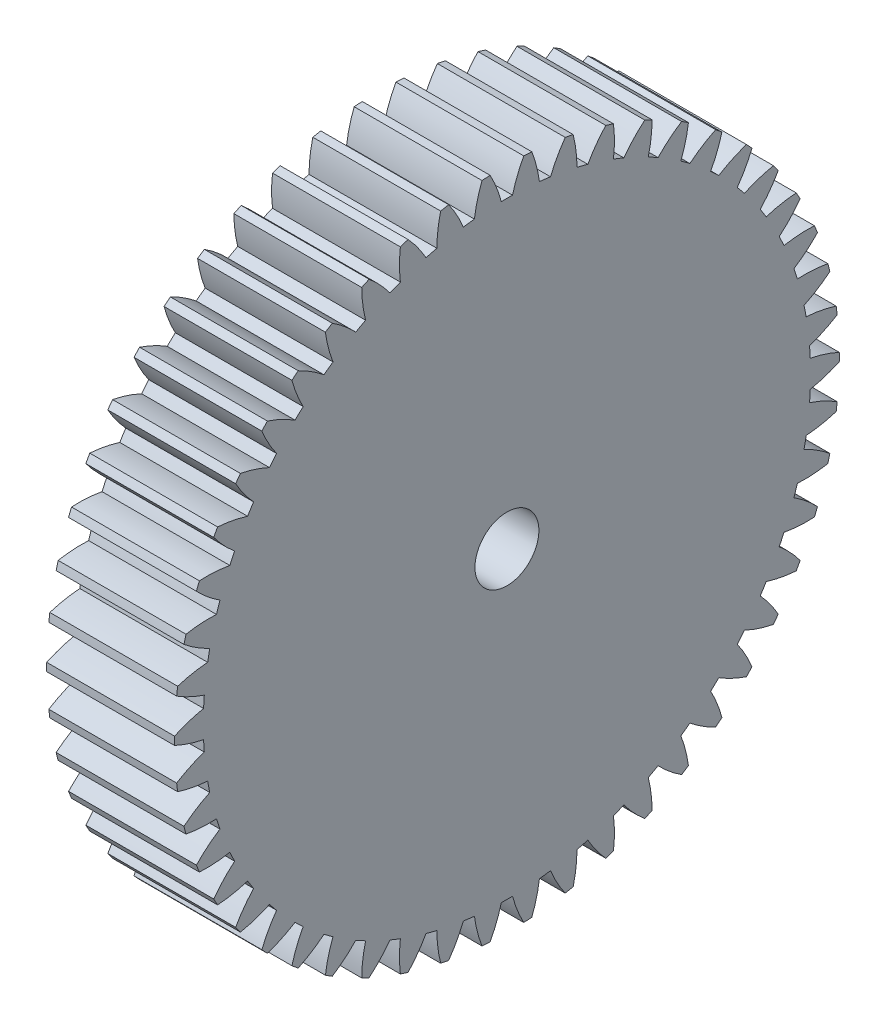
SolidWorks part; units mm, degrees
ref_plane "Plane1" through (0, 0, 0) normal (0, 0, 1) x (1, 0, 0)
ref_plane "Plane2" through (0, 0, 0) normal (0, 1, 0) x (1, 0, 0)
ref_plane "Plane3" through (0, 0, 0) normal (1, 0, 0) x (0, 0, -1)
other "Configuration Table"
sketch "HoldingSke" plane through (0, 0, 0) normal (0, 1, 0) x (1, 0, 0)
  line L0 (0, 0) -> (0.6428, -0.766)
  line L1 (-15, 0) -> (100, 0) construction
  line L2 (0, 0) -> (-2.1039, 2.3779)
  line L3 (0, 0) -> (-11.863, 4.5341)
  line L4 (0, 0) -> (5.5511, 6.6156)
  line L5 (0, 0) -> (-46.8476, -17.4728)
  line L6 (0, 0) -> (-8.2896, -5.593)
  line L7 (-2.1039, 2.3779) -> (8.6586, 51.2059)
  line L8 (-76.2, 54.61) -> (-75.3, 54.61)
  line L9 (-71.009, 38.7566) -> (-53.1078, 45.2721)
  line L10 (-76.2, 71.12) -> (104.1128, 71.12)
  line L11 (0, 0) -> (-10, 0)
  line L12 (-76.2, 101.6) -> (-76.162, 101.6)
  line L13 (24.9733, 27.94) -> (52.9518, 28.4284)
  line L14 (24.9733, 27.94) -> (24.9743, 27.94)
  line L15 (24.9733, 27.94) -> (100.4006, 29.5858)
  line L16 (-63.627, -1) -> (-12.827, -1)
  circle A0 centre (0, 0) radius 2.5
  circle A1 centre (0, 0) radius 23.749
  circle A2 centre (0, 0) radius 37.5
  circle A3 centre (0, 0) radius 2.5
  dimension "MHD" = 47.498
  dimension "Hub_dia" = 75
  dimension "Bore" = 5
  dimension "MBD" = 5
  dimension "Num_teeth" = 50
  dimension "Pitch" = 1
  dimension "Overall_len" = 50
  dimension "Show_teeth" = 50
  dimension "Thickness" = 10
  dimension "OAL" = 50.0001
  dimension "T_dim" = 0.9
  dimension "Ap" = 20
  dimension "H" = 19.05
  dimension "Pitch_radius" = 180.3128
  dimension "Width" = 10
  dimension "Backlash" = 0.038
  dimension "Addendum_fac" = 1
  dimension "Dedendum_fac" = 1.25
  dimension "Clearance_fac" = 0.25
  dimension "Dedendum_add" = 0.001
  dimension "Module" = 1
sketch "BasProSke" plane through (0, 0, 0) normal (0, 1, 0) x (1, 0, 0)
  line L0 (-10, 0) -> (60, 0) construction
  line L1 (0, 0) -> (0, 26)
  line L2 (0, 0) -> (10, 0)
  line L3 (10, 0) -> (10, 26)
  line L4 (10, 26) -> (0, 26)
  dimension "Thickness" = 10
  dimension "Diameter" = 52
revolve "Base-Revolve" add sketch "BasProSke" angle 360 about L0
sketch "TooCutSke" plane through (0, 0, 0) normal (1, 0, 0) x (0, 0, -1)
  line L1 (0, 0) -> (0, 107) construction
  line L2 (0, 0) -> (-0.8518, 24.9855) construction
  line L3 (0, 0) -> (-3.1382, 49.8807) construction
  line L4 (-0.8518, 24.9855) -> (-1.5691, 24.9404) construction
  arc A0 (0.4377, 23.745) -> (-0.4377, 23.745) centre (0, 0) ccw
  arc A1 (1.3294, 25.9914) -> (-1.3294, 25.9914) centre (0, 0) ccw
  circle A2 centre (0, 0) radius 25 construction
  circle A3 centre (0, 0) radius 23.4923 construction
  arc A4 (-0.4377, 23.745) -> (-1.3294, 25.9914) centre (-10.1099, 21.2056) ccw
  arc A5 (1.3294, 25.9914) -> (0.4377, 23.745) centre (10.1099, 21.2056) ccw
  dimension "Root_dia" = 47.498
  dimension "Overcut_dia" = 52.0508
  dimension "Pitch_dia" = 50
  dimension "Base_dia" = 46.9846
  dimension "Flank_rad" = 10
  dimension "Half_ang" = 3.6
  dimension "Half_CT" = 0.7188
extrude "ToothCut" cut sketch "TooCutSke" along normal through all
fillet "Breaks" [suppressed] radius 0.02
fillet "RootFillets" [suppressed] radius 0.251
pattern_circular "TeethCuts" count 50 every 7.2 about axis through (-10, 0, 0) along (1, 0, 0) of "ToothCut", "RootFillets", "Breaks"
sketch "HubNeaOneSke" plane through (0, 0, 0) normal (-1, 0, 0) x (0, 0, 1)
  circle A0 centre (0, 0) radius 23.749
  dimension "Diameter" = 47.498
extrude "HubNearOne" [suppressed] add sketch "HubNeaOneSke" along normal blind 40.0001
sketch "HubNeaBotSke" plane through (0, 0, 0) normal (-1, 0, 0) x (0, 0, 1)
  circle A0 centre (0, 0) radius 23.749
  dimension "Diameter" = 47.498
extrude "HubNearBoth" [suppressed] add sketch "HubNeaBotSke" along normal blind 20
ref_plane "FarPln" through (10, 0, 0) normal (1, 0, 0) x (0, 0, -1)
sketch "HubFarSke" plane through (10, 0, 0) normal (1, 0, 0) x (0, 0, -1)
  circle A0 centre (0, 0) radius 23.749
  dimension "Diameter" = 47.498
extrude "HubFar" [suppressed] add sketch "HubFarSke" along normal blind 20
sketch "BorSke" plane through (0, 0, 0) normal (1, 0, 0) x (0, 0, -1)
  circle A0 centre (0, 0) radius 2.5
  dimension "Diameter" = 5
extrude "Bore" cut sketch "BorSke" along normal mid plane 100.0001
sketch "KeySke" plane through (0, 0, 0) normal (1, 0, 0) x (0, 0, -1)
  line L0 (-1, 0) -> (-1, 3.4)
  line L1 (-1, 3.4) -> (1, 3.4)
  line L2 (1, 3.4) -> (1, 0)
  line L3 (0, 0) -> (0, 34) construction
  line L4 (-1, 0) -> (1, 0)
  dimension "Offset" = 3.4
  dimension "Width" = 2
extrude "Keyway" [suppressed] cut sketch "KeySke" along normal mid plane 100.0001
pattern_circular "Keyway2" [suppressed] count 2 every 90 about axis through (-10, 0, 0) along (1, 0, 0)
equation "' \"Module@HoldingSke\" = 6.35"
equation "' \"Num_teeth@HoldingSke\" = 12"
equation "' \"Ap@HoldingSke\" =  20"
equation "' \"Ap@HoldingSke\" = 20"
equation "' \"Width@HoldingSke\" = 0.5 * 25.4"
equation "' \"Hub_dia@HoldingSke\"= 1 * 25.4"
equation "' \"Hub_dia@HoldingSke\" = 1 * 25.4"
equation "' \"Overall_len@HoldingSke\" = 1.0 * 25.4"
equation "' \"Bore@HoldingSke\" = 0.75 * 25.4"
equation "' \"T_dim@HoldingSke\" = 0.1 * 25.4"
equation "' \"Width@KeySke\" = 0.25 * 25.4"
equation "' \"Show_teeth@HoldingSke\" = 13"
equation "' \"Backlash@HoldingSke\" = 0.009 * 25.4"
equation "' \"Addendum_fac@HoldingSke\" = 1.0"
equation "' \"Dedendum_fac@HoldingSke\" = 1.25"
equation "' \"Dedendum_add@HoldingSke\" = 0.00005 * 25.4"
equation "' \"Clearance_fac@HoldingSke\" = 0.25"
equation "\"Pitch@HoldingSke\" = 1 / \"Module@HoldingSke\""
equation "\"Overcut_dia@TooCutSke\" = (\"Num_teeth@HoldingSke\" + 2 * \"Addendum_fac@HoldingSke\") / \"Pitch@HoldingSke\" + 0.002 * 25.4"
equation "\"Pitch_dia@TooCutSke\" = \"Num_teeth@HoldingSke\" / \"Pitch@HoldingSke\""
equation "\"Base_dia@TooCutSke\" = \"Num_teeth@HoldingSke\" / \"Pitch@HoldingSke\" * cos((\"Ap@HoldingSke\"  * 3.14159265 / 180))"
equation "\"Root_dia@TooCutSke\" = (\"Num_teeth@HoldingSke\" + 2) / \"Pitch@HoldingSke\" - 2 * (\"Addendum_fac@HoldingSke\" + \"Dedendum_fac@HoldingSke\") / \"Pitch@HoldingSke\" - \"Dedendum_add@HoldingSke\" * 2"
equation "\"Half_ang@TooCutSke\" = 180 / \"Num_teeth@HoldingSke\""
equation "\"Half_CT@TooCutSke\" = \"Num_teeth@HoldingSke\" / \"Pitch@HoldingSke\" * sin((3.14159265 / 2 / \"Num_teeth@HoldingSke\")) / 2 - 7 * \"Backlash@HoldingSke\" / 4"
equation "\"Flank_rad@TooCutSke\" = \"Num_teeth@HoldingSke\" / \"Pitch@HoldingSke\" / 5"
equation "\"Radius@RootFillets\" = \"Clearance_fac@HoldingSke\" / \"Pitch@HoldingSke\" + \"Dedendum_add@HoldingSke\""
equation "\"Break_rad@Breaks\" = 0.02 / \"Pitch@HoldingSke\""
equation "\"Thickness@HoldingSke\" = \"Width@HoldingSke\""
equation "\"OAL@HoldingSke\" = \"Thickness@HoldingSke\""
equation "\"MHD@HoldingSke\" = (\"Num_teeth@HoldingSke\" + 2) / \"Pitch@HoldingSke\" - 2 * (\"Addendum_fac@HoldingSke\" + \"Dedendum_fac@HoldingSke\")  / \"Pitch@HoldingSke\" - \"Dedendum_add@HoldingSke\" * 2"
equation "\"MBD@HoldingSke\" = (\"Num_teeth@HoldingSke\" + 2) / \"Pitch@HoldingSke\" - 2 * (\"Addendum_fac@HoldingSke\" + \"Dedendum_fac@HoldingSke\")  / \"Pitch@HoldingSke\" - \"Dedendum_add@HoldingSke\" * 2 - 0.002 * 25.4"
equation "\"MHD@HoldingSke\" = ((sgn( \"MHD@HoldingSke\" - \"Hub_dia@HoldingSke\" )-1)*( \"MHD@HoldingSke\" - \"Hub_dia@HoldingSke\" ))/-2+ \"Hub_dia@HoldingSke\""
equation "\"MBD@HoldingSke\" = ((sgn( \"MBD@HoldingSke\" - \"Bore@HoldingSke\" )-1)*( \"MBD@HoldingSke\" - \"Bore@HoldingSke\" ))/-2+ \"Bore@HoldingSke\""
equation "\"OAL@HoldingSke\" = ((sgn( \"OAL@HoldingSke\" - \"Overall_len@HoldingSke\" )+1)*( \"OAL@HoldingSke\" - \"Overall_len@HoldingSke\" ))/2 + \"Overall_len@HoldingSke\" + 0.000002 * 25.4"
equation "\"Num_teeth@TeethCuts\" = int( \"Show_teeth@HoldingSke\" ) + 1"
equation "\"Num_teeth@TeethCuts\" = ((sgn( \"Num_teeth@TeethCuts\" - \"Num_teeth@HoldingSke\" )-1)*( \"Num_teeth@TeethCuts\" - \"Num_teeth@HoldingSke\" ))/-2+ \"Num_teeth@HoldingSke\""
equation "\"Num_teeth@TeethCuts\" = ((sgn( \"Num_teeth@TeethCuts\" - 2.0)+1)*( \"Num_teeth@TeethCuts\" - 2.0))/2 +2.0"
equation "\"Angle@TeethCuts\" = 360.0 / \"Num_teeth@HoldingSke\""
equation "\"Diameter@BasProSke\" = (\"Num_teeth@HoldingSke\" + 2 * \"Addendum_fac@HoldingSke\") / \"Pitch@HoldingSke\""
equation "\"Thickness@BasProSke\"  = \"Thickness@HoldingSke\""
equation "' \"Fillet_rad@BasProSke\" =  \"Thickness@HoldingSke\" * 0.05"
equation "' \"Fillet_rad@BasProSke\" = \"Thickness@HoldingSke\" * 0.05"
equation "\"MHD@HoldingSke\" = ((sgn( \"MHD@HoldingSke\" - \"Root_dia@TooCutSke\" )-1)*( \"MHD@HoldingSke\" - \"Root_dia@TooCutSke\" ))/-2+ \"Root_dia@TooCutSke\""
equation "\"Diameter@HubNeaOneSke\" = \"MHD@HoldingSke\""
equation "\"Length@HubNearOne\" = \"OAL@HoldingSke\" - \"Thickness@BasProSke\""
equation "\"Diameter@HubNeaBotSke\" = \"MHD@HoldingSke\""
equation "\"Length@HubNearBoth\" = ( \"OAL@HoldingSke\" - \"Thickness@BasProSke\" ) / 2.0"
equation "\"Thickness@FarPln\" = \"Thickness@BasProSke\""
equation "\"Diameter@HubFarSke\" = \"MHD@HoldingSke\""
equation "\"Length@HubFar\" = ( \"OAL@HoldingSke\" - \"Thickness@BasProSke\" ) / 2.0"
equation "\"Diameter@BorSke\" = \"MBD@HoldingSke\""
equation "\"D1@Bore\" = \"OAL@HoldingSke\" * 2.0"
equation "\"D1@Keyway\" = \"OAL@HoldingSke\" * 2.0"
equation "\"Offset@KeySke\" = \"T_dim@HoldingSke\" + \"MBD@HoldingSke\" / 2.0"
